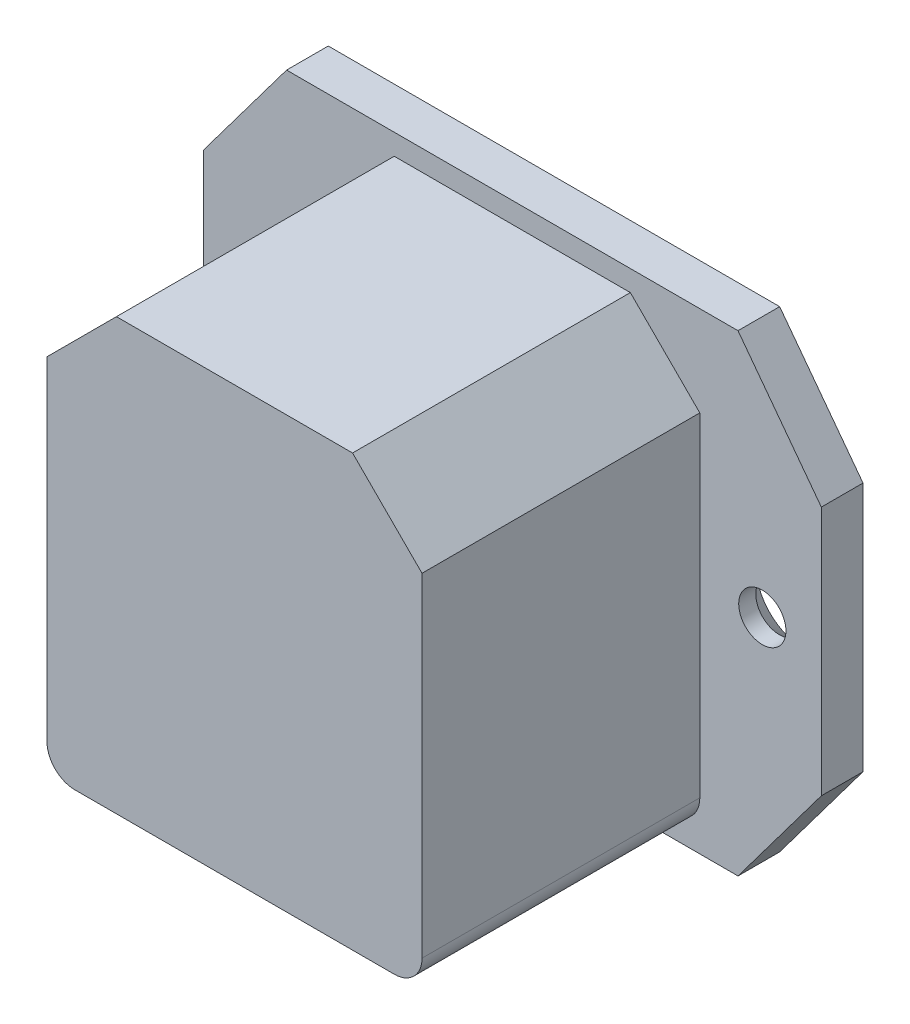
SolidWorks part; units mm, degrees
ref_plane "Ebene vorne" through (0, 0, 0) normal (0, 0, 1) x (1, 0, 0)
ref_plane "Ebene oben" through (0, 0, 0) normal (0, 1, 0) x (1, 0, 0)
ref_plane "Ebene rechts" through (0, 0, 0) normal (1, 0, 0) x (0, 0, -1)
sketch "Skizze1" plane through (0, 0, 0) normal (0, 0, 1) x (1, 0, 0)
  line L1 (-13.5, -15.5) -> (13.5, -15.5)
  line L2 (-13.5, -15.5) -> (-13.5, 15.5)
  line L3 (-13.5, 15.5) -> (13.5, 15.5)
  line L4 (13.5, -15.5) -> (13.5, 15.5)
  line L5 (-13.5, -15.5) -> (13.5, 15.5) construction
  line L6 (-13.5, 15.5) -> (13.5, -15.5) construction
  point P0 (0, 0)
  dimension "D1" = 27
  dimension "D2" = 31
extrude "Aufsatz-Linear austragen1" add sketch "Skizze1" along normal blind 20
sketch "Skizze2" plane through (0, 0, 0) normal (0, 0, 1) x (1, 0, 0)
  line L0 (0, 17) -> (0, 0) construction
  line L1 (16.25, 17) -> (-16.25, 17)
  line L2 (22.25, -9) -> (22.25, 9)
  line L3 (0, 0) -> (22.25, 0) construction
  line L4 (-22.25, 9) -> (-16.25, 17)
  line L5 (22.25, 9) -> (16.25, 17)
  line L6 (-22.25, -9) -> (-22.25, 9)
  line L7 (-22.25, -9) -> (-16.25, -17)
  line L8 (22.25, -9) -> (16.25, -17)
  line L9 (16.25, -17) -> (-16.25, -17)
  point P10 (-22.25, 0)
  dimension "D3" = 8
  dimension "D1" = 44.5
  dimension "D2" = 34
  dimension "D5" = 6
extrude "Aufsatz-Linear austragen2" add sketch "Skizze2" against normal blind 3
hole_wizard "Formsenkung für M3 Senkschraube mit Innensechskant1" positions "Skizze4" profile "Skizze3" countersink size "M3" standard "DIN" end condition up to next
sketch "Skizze4" plane through (0, 0, -3) normal (0, 0, -1) x (-1, 0, 0)
  line L0 (0, 0) -> (-18, 0) construction
  line L3 (0, 0) -> (18, 0) construction
  point P22 (-18, 0)
  point P25 (18, 0)
  dimension "D1" = 36
sketch "Skizze3" plane through (18, 0, -3) normal (1, 0, 0) x (0, 1, 0)
  line L0 (0, 0) -> (0, 3)
  line L1 (0, 3) -> (1.7, 3)
  line L2 (1.7, 3) -> (1.7, 1.77)
  line L3 (1.7, 1.77) -> (3.47, 0)
  line L5 (3.47, 0) -> (0, 0)
  line L6 (-1.7, 1.77) -> (-3.47, 0) construction
  line L11 (0, -6.35) -> (0, 107.95) construction
  dimension "Bohrerdurchmesser" = 3.4
  dimension "Bohrungstiefe" = 3
  dimension "Senkdurchmesser (Oben)" = 6.94
  dimension "Senkwinkel (Oben)" = 90
sketch "Skizze5" plane through (0, 0, -3) normal (0, 0, -1) x (-1, 0, 0)
  line L0 (0, 0) -> (0, 14) construction
  line L1 (7.25, 14) -> (-7.25, 14)
  line L2 (-7.25, 14) -> (-12.25, 9)
  line L3 (-12.25, 9) -> (-12.25, -2)
  line L4 (-12.25, -2) -> (12.25, -2)
  line L5 (0, -2) -> (0, 0) construction
  line L6 (-13.5, 15.5) -> (13.5, 15.5) construction
  line L7 (12.25, 9) -> (12.25, -2)
  line L8 (7.25, 14) -> (12.25, 9)
  dimension "D1" = 24.5
  dimension "D2" = 16
  dimension "D3" = 5
  dimension "D4" = 5
  dimension "D5" = 1.5
extrude "Schnitt-Linear austragen1" cut sketch "Skizze5" against normal blind 18
chamfer "Fase1" distance 5 angle 45 2 edges at (13.5, 15.5, 10) (-13.5, 15.5, 10)
fillet "Verrundung1" radius 2 2 edges at (13.5, -15.5, 10) (-13.5, -15.5, 10)
